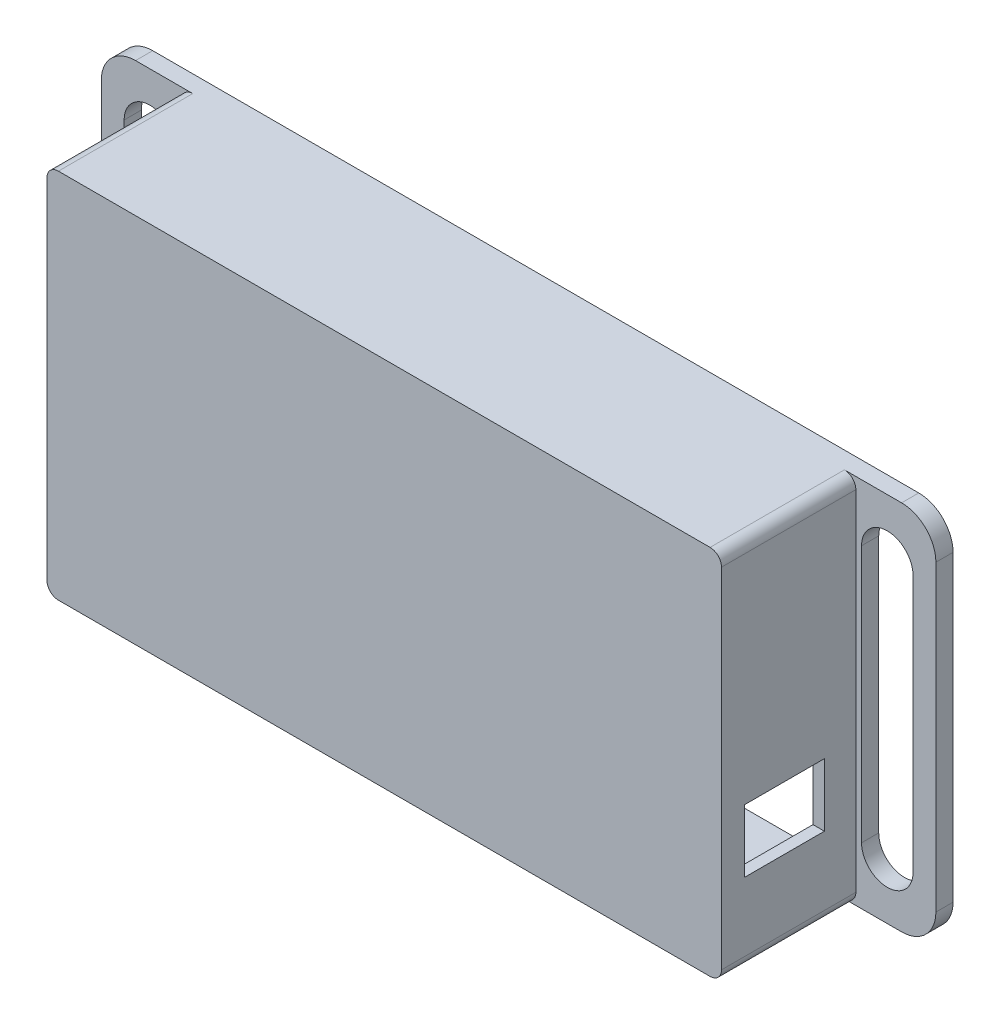
SolidWorks part; units mm, degrees
ref_plane "Front" through (0, 0, 0) normal (0, 0, 1) x (1, 0, 0)
ref_plane "Top" through (0, 0, 0) normal (0, 1, 0) x (1, 0, 0)
ref_plane "Right" through (0, 0, 0) normal (1, 0, 0) x (0, 0, -1)
sketch "Sketch1" plane through (0, 0, 0) normal (0, 0, 1) x (1, 0, 0)
  line L1 (-56.125, 30) -> (56.125, 30)
  line L2 (-56.125, 30) -> (-56.125, -30)
  line L3 (-56.125, -30) -> (56.125, -30)
  line L4 (56.125, 30) -> (56.125, -30)
  line L5 (-56.125, 30) -> (56.125, -30) construction
  line L6 (-56.125, -30) -> (56.125, 30) construction
  point P0 (0, 0)
  dimension "D1" = 112.25
  dimension "D2" = 60
sketch "Sketch2" plane through (0, 0, 0) normal (0, 0, 1) x (1, 0, 0)
  line L0 (-59, 32.5) -> (-59, -32.5)
  line L1 (-57, 30.5) -> (57, 30.5) construction
  line L2 (-57, 30.5) -> (-57, -30.5) construction
  line L3 (-57, -30.5) -> (57, -30.5) construction
  line L4 (57, 30.5) -> (57, -30.5) construction
  line L5 (-57, 30.5) -> (57, -30.5) construction
  line L6 (-57, -30.5) -> (57, 30.5) construction
  line L7 (-59, -32.5) -> (59, -32.5)
  line L8 (59, 32.5) -> (59, -32.5)
  line L9 (-59, 32.5) -> (59, 32.5)
  point P0 (0, 0)
  dimension "D1" = 61
  dimension "D2" = 114
  dimension "D3" = 2
extrude "Boss-Extrude2" add sketch "Sketch2" along normal blind 1.5
sketch "Sketch4" plane through (0, 0, 0) normal (0, 0, 1) x (1, 0, 0)
  line L0 (57, -30.5) -> (57, 30.5)
  line L1 (-59, -32.5) -> (59, -32.5)
  line L2 (-59, -32.5) -> (-59, 32.5)
  line L3 (-59, 32.5) -> (59, 32.5)
  line L4 (59, -32.5) -> (59, 32.5)
  line L5 (-57, 30.5) -> (57, 30.5)
  line L6 (-57, -30.5) -> (-57, 30.5)
  line L7 (-57, -30.5) -> (57, -30.5)
  dimension "D1" = 2
extrude "Boss-Extrude3" add sketch "Sketch4" against normal blind 25
sketch "Sketch6" plane through (0, 0, -25) normal (0, 0, -1) x (-1, 0, 0)
  line L0 (64.5, -22.5) -> (64.5, 22.5) construction
  line L1 (59, 32.5) -> (73, 32.5)
  line L2 (59, 32.5) -> (59, -32.5)
  line L3 (59, -32.5) -> (73, -32.5)
  line L4 (73, 32.5) -> (73, -32.5)
  line L5 (60, -22.5) -> (60, 22.5)
  line L6 (69, -22.5) -> (69, 22.5)
  line L7 (0, 0) -> (64.5, 0) construction
  line L8 (64.5, -22.5) -> (64.5, -32.5) construction
  arc A0 (60, -22.5) -> (69, -22.5) centre (64.5, -22.5) ccw
  arc A1 (69, 22.5) -> (60, 22.5) centre (64.5, 22.5) ccw
  point P8 (64.5, 0)
  dimension "D1" = 4
  dimension "D2" = 9
  dimension "D3" = 45
  dimension "D4" = 1
extrude "Boss-Extrude4" add sketch "Sketch6" against normal blind 3
fillet "Fillet1" radius 6 2 edges at (-73, -32.5, -23.5) (-73, 32.5, -23.5)
mirror "Mirror1" about plane through (0, 0, 0) normal (1, 0, 0) of "Fillet1", "Boss-Extrude4"
fillet "Fillet2" radius 2 4 edges
fillet "Fillet3" radius 1 4 edges at (-57, -30.5, -12.5) (-57, 30.5, -12.5) (57, 30.5, -12.5) (57, -30.5, -12.5)
sketch "Sketch7" plane through (59, 0, 0) normal (1, 0, 0) x (0, 0, -1)
  line L1 (2.5, -7.5) -> (16.5, -7.5)
  line L2 (2.5, -7.5) -> (2.5, -18.5)
  line L3 (2.5, -18.5) -> (16.5, -18.5)
  line L4 (16.5, -7.5) -> (16.5, -18.5)
  dimension "D1" = 2.5
  dimension "D2" = 14
  dimension "D3" = 11
  dimension "D4" = 7.5
extrude "Cut-Extrude1" cut sketch "Sketch7" against normal blind 10
